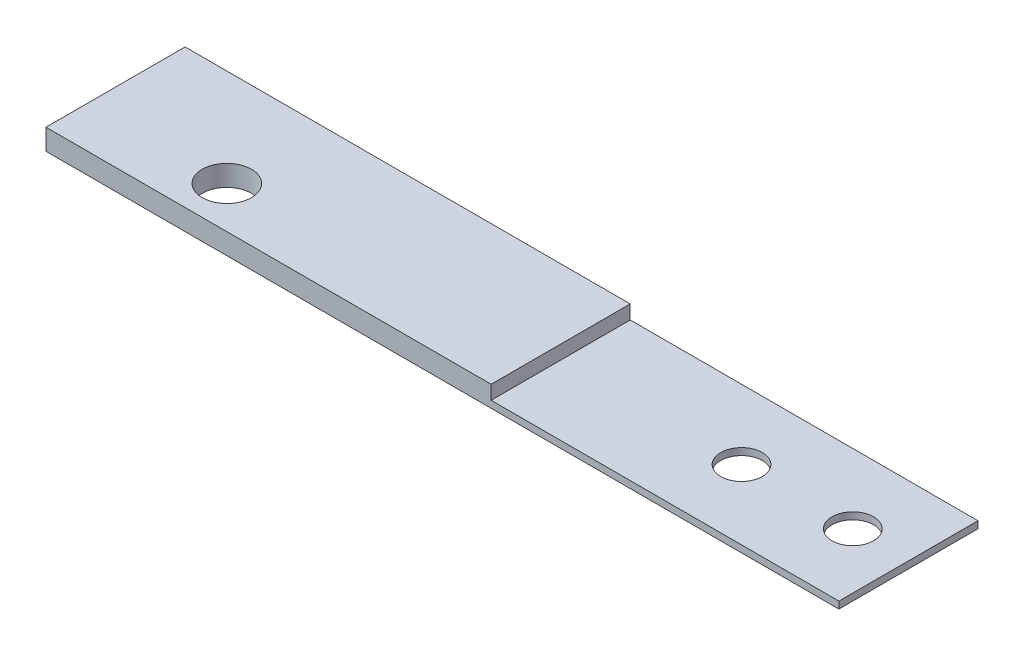
SolidWorks part; units mm, degrees
ref_plane "Front Plane" through (0, 0, 0) normal (0, 0, 1) x (1, 0, 0)
ref_plane "Top Plane" through (0, 0, 0) normal (0, 1, 0) x (1, 0, 0)
ref_plane "Right Plane" through (0, 0, 0) normal (1, 0, 0) x (0, 0, -1)
sketch "Sketch1" plane through (0, 0, 0) normal (0, 1, 0) x (1, 0, 0)
  line L1 (0, 0) -> (72.39, 0)
  line L2 (0, 0) -> (0, -12.7)
  line L3 (0, -12.7) -> (72.39, -12.7)
  line L4 (72.39, 0) -> (72.39, -12.7)
  dimension "D1" = 72.39
  dimension "D2" = 12.7
extrude "Boss-Extrude1" add sketch "Sketch1" along normal blind 0.635 contours L1 L4 L3 L2
sketch "Sketch2" plane through (0, 0.635, 0) normal (0, 1, 0) x (1, 0, 0)
  line L0 (0, -12.7) -> (72.39, -12.7) construction
  line L1 (0, 0) -> (40.64, 0)
  line L2 (0, 0) -> (0, -12.7)
  line L3 (0, -12.7) -> (40.64, -12.7)
  line L4 (40.64, 0) -> (40.64, -12.7)
  line L5 (72.39, 0) -> (72.39, -12.7) construction
  dimension "D1" = 31.75
extrude "Boss-Extrude2" add sketch "Sketch2" along normal blind 1.27
sketch "Sketch3" plane through (0, 0, 0) normal (0, -1, 0) x (1, 0, 0)
  line L0 (72.39, 0) -> (72.39, 12.7) construction
  line L1 (0, 0) -> (0, 12.7) construction
  line L3 (0, 12.7) -> (72.39, 12.7) construction
  point P0 (67.31, 6.35)
  point P1 (57.15, 6.35)
  point P2 (12.7, 8.89)
  dimension "D1" = 5.08
  dimension "D2" = 10.16
  dimension "D3" = 12.7
  dimension "D4" = 3.81
  dimension "D5" = 6.35
  dimension "D6" = 6.35
hole_wizard "#6 Clearance Hole1" positions "Sketch4" profile "Sketch5" hole size "#6" standard "ANSI Inch" end condition through all
sketch "Sketch4" plane through (0, 0, 0) normal (0, -1, 0) x (-1, 0, 0)
  point P0 (-67.31, -6.35)
  point P3 (-57.15, -6.35)
sketch "Sketch5" plane through (67.31, 0, 6.35) normal (1, 0, 0) x (0, 0, -1)
  line L0 (0, 0) -> (0, 1.905)
  line L1 (0, 1.905) -> (1.8986, 1.905)
  line L2 (1.8986, 1.905) -> (1.8986, 0)
  line L5 (1.8986, 0) -> (0, 0)
  line L11 (0, -6.35) -> (0, 107.95) construction
  dimension "Thru Hole Dia." = 3.7973
  dimension "Thru Hole Depth" = 1.905
hole_wizard "#8 Clearance Hole1" positions "Sketch6" profile "Sketch7" hole size "#8" standard "ANSI Inch" end condition through all
sketch "Sketch6" plane through (0, 0, 0) normal (0, -1, 0) x (-1, 0, 0)
  point P0 (-12.7, -8.89)
sketch "Sketch7" plane through (12.7, 0, 8.89) normal (1, 0, 0) x (0, 0, -1)
  line L0 (0, 0) -> (0, 1.905)
  line L1 (0, 1.905) -> (2.2479, 1.905)
  line L2 (2.2479, 1.905) -> (2.2479, 0)
  line L5 (2.2479, 0) -> (0, 0)
  line L11 (0, -6.35) -> (0, 107.95) construction
  dimension "Thru Hole Dia." = 4.4958
  dimension "Thru Hole Depth" = 1.905
sketch "Sketch9" plane through (0, 0, 0) normal (-1, 0, 0) x (0, 0, 1)
  line L0 (0, 0) -> (0.2933, 0.508)
  line L1 (0.2933, 0.508) -> (0.5866, 0)
  line L2 (0, 0) -> (12.7, 0) construction
  line L3 (0.5866, 0) -> (0.8799, 0.508)
  line L4 (0.8799, 0.508) -> (1.1732, 0)
  line L5 (1.27, 0) -> (1.5633, 0.508)
  line L6 (1.5633, 0.508) -> (1.8566, 0)
  line L7 (1.8566, 0) -> (2.1499, 0.508)
  line L8 (2.1499, 0.508) -> (2.4432, 0)
  line L9 (2.54, 0) -> (2.8333, 0.508)
  line L10 (2.8333, 0.508) -> (3.1266, 0)
  line L11 (3.1266, 0) -> (3.4199, 0.508)
  line L12 (3.4199, 0.508) -> (3.7132, 0)
  line L13 (3.81, 0) -> (4.1033, 0.508)
  line L14 (4.1033, 0.508) -> (4.3966, 0)
  line L15 (4.3966, 0) -> (4.6899, 0.508)
  line L16 (4.6899, 0.508) -> (4.9832, 0)
  line L17 (5.08, 0) -> (5.3733, 0.508)
  line L18 (5.3733, 0.508) -> (5.6666, 0)
  line L19 (5.6666, 0) -> (5.9599, 0.508)
  line L20 (5.9599, 0.508) -> (6.2532, 0)
  line L21 (6.35, 0) -> (6.6433, 0.508)
  line L22 (6.6433, 0.508) -> (6.9366, 0)
  line L23 (6.9366, 0) -> (7.2299, 0.508)
  line L24 (7.2299, 0.508) -> (7.5232, 0)
  line L25 (7.62, 0) -> (7.9133, 0.508)
  line L26 (7.9133, 0.508) -> (8.2066, 0)
  line L27 (8.2066, 0) -> (8.4999, 0.508)
  line L28 (8.4999, 0.508) -> (8.7932, 0)
  line L29 (8.89, 0) -> (9.1833, 0.508)
  line L30 (9.1833, 0.508) -> (9.4766, 0)
  line L31 (9.4766, 0) -> (9.7699, 0.508)
  line L32 (9.7699, 0.508) -> (10.0632, 0)
  line L33 (10.16, 0) -> (10.4533, 0.508)
  line L34 (10.4533, 0.508) -> (10.7466, 0)
  line L35 (10.7466, 0) -> (11.0399, 0.508)
  line L36 (11.0399, 0.508) -> (11.3332, 0)
  line L37 (11.43, 0) -> (11.7233, 0.508)
  line L38 (11.7233, 0.508) -> (12.0166, 0)
  line L39 (12.0166, 0) -> (12.3099, 0.508)
  line L40 (12.3099, 0.508) -> (12.6032, 0)
  line L41 (0, 0) -> (12.6032, 0)
  line M5 (0, 0) -> (12.7, 0)
  dimension "D1" = 60
  dimension "D2" = 60
  dimension "D3" = 0.508
  dimension "D4" = 60
  dimension "D5" = 0.508
  dimension "D6" = 60
  dimension "D7" = 10
extrude "Cut-Extrude6" cut sketch "Sketch9" against normal blind 10.16 and the other way through all contours L6 L5 M5 | L8 L7 M5 | L4 L3 M5 | L1 L0 M5 | L10 L9 M5 | L12 L11 M5 | L14 L13 M5 | L16 L15 M5 | L18 L17 M5 | L20 L19 M5 | L22 L21 M5 | L24 L23 M5 | L26 L25 M5 | L28 L27 M5 | L30 L29 M5 | L32 L31 M5 | L34 L33 M5 | L36 L35 M5 | L38 L37 M5 | L40 L39 M5
